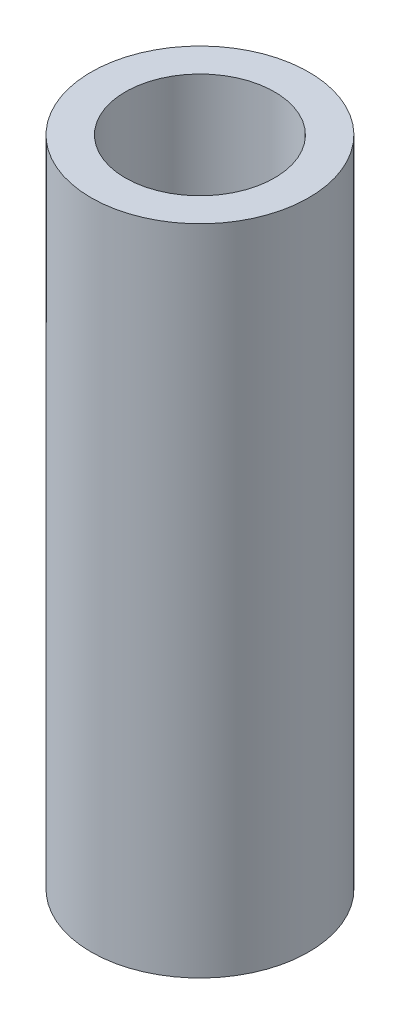
SolidWorks part; units mm, degrees
ref_plane "Front Plane" through (0, 0, 0) normal (0, 0, 1) x (1, 0, 0)
ref_plane "Top Plane" through (0, 0, 0) normal (0, 1, 0) x (1, 0, 0)
ref_plane "Right Plane" through (0, 0, 0) normal (1, 0, 0) x (0, 0, -1)
sketch "Sketch1" plane through (0, 0, 0) normal (0, 1, 0) x (1, 0, 0)
  circle A0 centre (0, 0) radius 3.2639
  circle A1 centre (0, 0) radius 4.7625
  dimension "D1" = 9.525
  dimension "D2" = 6.5278
extrude "Boss-Extrude1" add sketch "Sketch1" along normal blind 28.575
